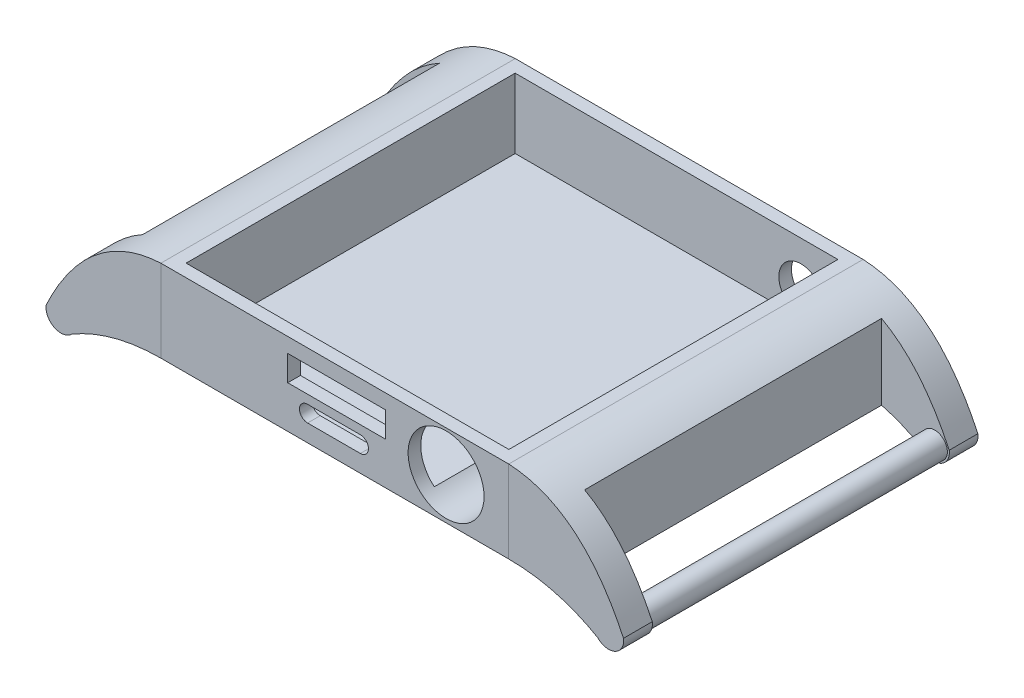
SolidWorks part; units mm, degrees
ref_plane "Front Plane" through (0, 0, 0) normal (0, 0, 1) x (1, 0, 0)
ref_plane "Top Plane" through (0, 0, 0) normal (0, 1, 0) x (1, 0, 0)
ref_plane "Right Plane" through (0, 0, 0) normal (1, 0, 0) x (0, 0, -1)
sketch "Sketch1" plane through (0, 0, 0) normal (0, 1, 0) x (1, 0, 0)
  line L1 (-27.485, -28) -> (27.485, -28)
  line L2 (-27.485, -28) -> (-27.485, 28)
  line L3 (-27.485, 28) -> (27.485, 28)
  line L4 (27.485, -28) -> (27.485, 28)
  line L5 (-27.485, -28) -> (27.485, 28) construction
  line L6 (-27.485, 28) -> (27.485, -28) construction
  point P0 (0, 0)
extrude "Boss-Extrude1" add sketch "Sketch1" along normal blind 13
sketch "Sketch2" plane through (0, 13, 0) normal (0, 1, 0) x (1, 0, 0)
  line L1 (-25.5, -26) -> (25.5, -26)
  line L2 (-25.5, -26) -> (-25.5, 26)
  line L3 (-25.5, 26) -> (25.5, 26)
  line L4 (25.5, -26) -> (25.5, 26)
  line L5 (-25.5, -26) -> (25.5, 26) construction
  line L6 (-25.5, 26) -> (25.5, -26) construction
  point P0 (0, 0)
extrude "Cut-Extrude1" cut sketch "Sketch2" against normal blind 11
sketch "Sketch3" plane through (0, 0, 28) normal (0, 0, 1) x (1, 0, 0)
  line L0 (4.037, 4.0013) -> (-4.303, 4.0013) construction
  line L3 (4.037, 2.7213) -> (-4.303, 2.7213)
  line L4 (4.037, 5.2813) -> (-4.303, 5.2813)
  circle A0 centre (17.5848, 6.5901) radius 6
  arc A3 (4.037, 2.7213) -> (4.037, 5.2813) centre (4.037, 4.0013) ccw
  arc A4 (-4.303, 5.2813) -> (-4.303, 2.7213) centre (-4.303, 4.0013) ccw
  point P4 (-0.133, 4.0013)
  point P9 (17.5848, 6.5901)
extrude "Cut-Extrude2" cut sketch "Sketch3" against normal blind 11
sketch "Sketch4" plane through (0, 0, 28) normal (0, 0, 1) x (1, 0, 0)
  line L5 (8.0104, 10.6761) -> (-7.4389, 10.6761)
  line L6 (8.0104, 10.6761) -> (8.0104, 6.6593)
  line L7 (8.0104, 6.6593) -> (-7.4389, 6.6593)
  line L8 (-7.4389, 10.6761) -> (-7.4389, 6.6593)
extrude "Cut-Extrude3" cut sketch "Sketch4" against normal blind 11
sketch "Sketch5" plane through (0, 0, -28) normal (0, 0, -1) x (-1, 0, 0)
  circle A0 centre (-19.6638, 5.9871) radius 3.5
extrude "Cut-Extrude4" cut sketch "Sketch5" against normal blind 11
sketch "Sketch6" plane through (0, 0, -28) normal (0, 0, -1) x (-1, 0, 0)
  line L1 (-27.485, 0) -> (-27.485, 13)
  arc A0 (-45.6181, -1.784) -> (-41.578, -3.7529) centre (-43.2726, -2.1007) ccw
  spline S0 degree 2 poles (-27.485, 0) (-35.193, -0.027) (-41.578, -3.7529) knots 0 0 0 1 1 1
  spline S2 degree 2 poles (-45.6181, -1.784) (-38.9657, 12.3896) (-27.485, 13) knots 0 0 0 0.917429 0.917429 0.917429
extrude "Boss-Extrude2" add sketch "Sketch6" against normal up to vertex (56 mm away) separate body
ref_plane "Plane1" through (0, 0, 0) normal (1, 0, 0) x (0, 0, -1)
sketch "Sketch7" plane through (0, 0, 0) normal (0, 1, 0) x (1, 0, 0)
  line L1 (34.9284, 23.4736) -> (45.9841, 23.4736)
  line L2 (34.9284, 23.4736) -> (34.9284, -23.4515)
  line L3 (34.9284, -23.4515) -> (45.9841, -23.4515)
  line L4 (45.9841, 23.4736) -> (45.9841, -23.4515)
extrude "Cut-Extrude5" cut sketch "Sketch7" against normal blind 11 and the other way blind 11
sketch "Sketch8" plane through (0, 0, -23.4736) normal (0, 0, 1) x (1, 0, 0)
  circle A0 centre (43.3265, -2.1626) radius 2
  point P2 (0, 0)
  point P3 (0, 0)
  point P4 (43.3265, -2.1626)
  point P5 (0, 0)
  point P6 (0, 0)
extrude "Boss-Extrude3" add sketch "Sketch8" along normal up to vertex (46.9251 mm away) separate body
mirror "Mirror2" about plane through (0, 0, 0) normal (1, 0, 0) of bodies 108 109
